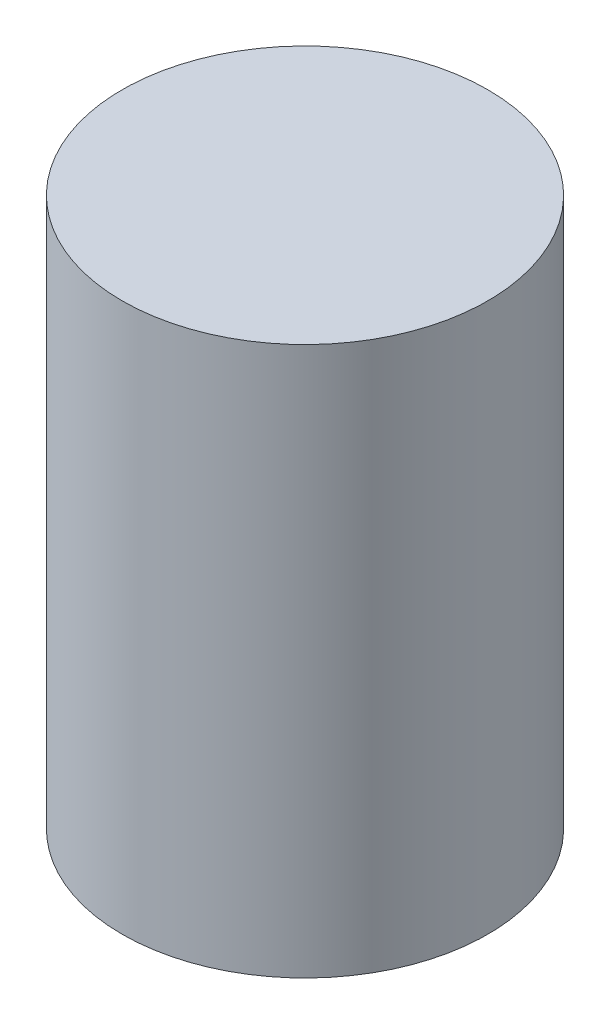
SolidWorks part; units mm, degrees
ref_plane "Front Plane" through (0, 0, 0) normal (0, 0, 1) x (1, 0, 0)
ref_plane "Top Plane" through (0, 0, 0) normal (0, 1, 0) x (1, 0, 0)
ref_plane "Right Plane" through (0, 0, 0) normal (1, 0, 0) x (0, 0, -1)
sketch "Sketch1" plane through (0, 0, 0) normal (0, 1, 0) x (1, 0, 0)
  circle A0 centre (0, 0) radius 3
  dimension "D1" = 6
extrude "Boss-Extrude1" add sketch "Sketch1" along normal blind 9
